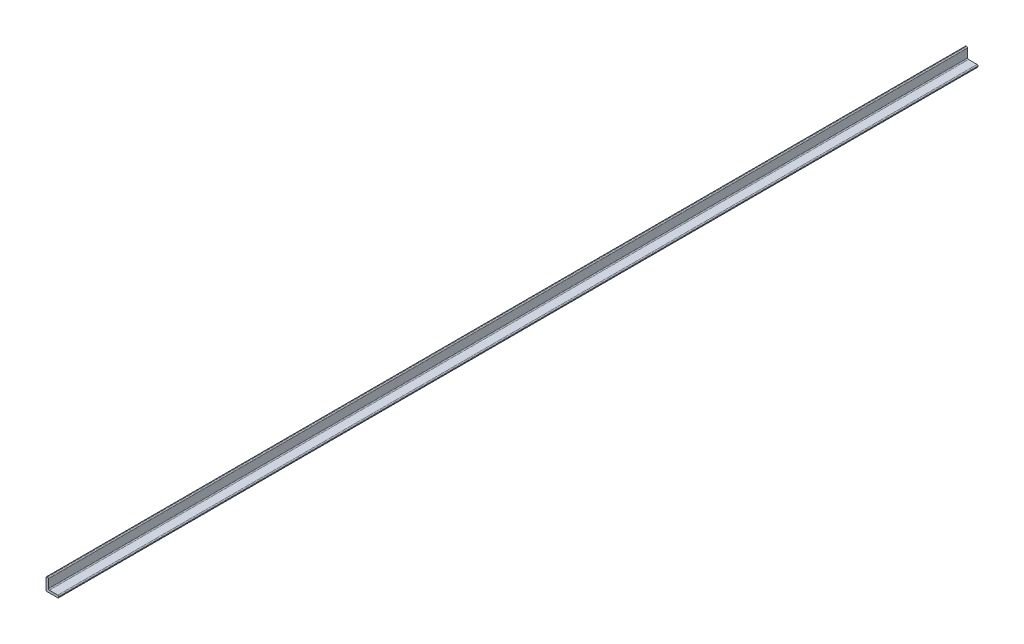
SolidWorks part; units mm, degrees
ref_plane "Front Plane" through (0, 0, 0) normal (0, 0, 1) x (1, 0, 0)
ref_plane "Top Plane" through (0, 0, 0) normal (0, 1, 0) x (1, 0, 0)
ref_plane "Right Plane" through (0, 0, 0) normal (1, 0, 0) x (0, 0, -1)
sketch "Sketch1" plane through (0, 0, 0) normal (0, 0, 1) x (1, 0, 0)
  line L0 (0, -12.7) -> (0, 12.7) construction
  line L1 (12.7, 0) -> (-12.7, 0) construction
  line L2 (-12.7, 12.7) -> (-12.7, -12.7) construction
  line L3 (-12.7, -12.7) -> (12.7, -12.7) construction
  line L4 (12.7, -12.7) -> (12.7, -7.9375) construction
  line L5 (12.7, -7.9375) -> (-7.9375, -7.9375) construction
  line L6 (-7.9375, -7.9375) -> (-7.9375, 12.7) construction
  line L7 (-7.9375, 12.7) -> (-12.7, 12.7) construction
  line L8 (-7.9375, -7.9375) -> (-12.7, -7.9375) construction
  line L9 (-7.9375, -7.9375) -> (-7.9375, -12.7) construction
  point P4 (0, 0)
  point P8 (0, 0)
  point P14 (12.7, -8.0645)
  dimension "Wall Thickness" = 4.7625
  dimension "Outside Height" = 25.4
  dimension "Outside Width" = 25.4
  dimension "Inside Width" = 20.6375
  dimension "Inside Height" = 20.6375
  dimension "Finish Thickness" = 0.254
sketch "Sketch2" plane through (0, 0, 0) normal (1, 0, 0) x (0, 0, -1)
  line L0 (914.4, 0) -> (-914.4, 0) construction
  line L1 (914.4, -12.7) -> (-914.4, -12.7) construction
  point P0 (-882.65, 0)
  point P4 (0, 0)
  point P5 (882.65, 0)
  point P9 (0, -12.7)
  dimension "Length" = 1828.8
  dimension "D1" = 31.75
  dimension "D2" = 31.75
sketch "Sketch4" plane through (0, 0, 0) normal (0, 0, 1) x (1, 0, 0)
  line L0 (-7.9375, -7.9375) -> (-7.9375, 12.7) construction
  line L1 (12.7, -7.9375) -> (-7.9375, -7.9375) construction
  line L2 (12.7, -12.7) -> (12.7, -7.9375) construction
  line L3 (-12.7, -12.7) -> (12.7, -12.7) construction
  line L4 (-12.7, 12.7) -> (-12.7, -12.7) construction
  line L5 (-7.9375, 12.7) -> (-12.7, 12.7) construction
  line L6 (-7.9375, -6.0325) -> (-7.9375, 12.7)
  line L7 (12.7, -7.9375) -> (-6.0325, -7.9375)
  line L8 (12.7, -12.7) -> (12.7, -7.9375)
  line L9 (-12.7, -12.7) -> (12.7, -12.7)
  line L10 (-12.7, 12.7) -> (-12.7, -12.7)
  line L11 (-7.9375, 12.7) -> (-12.7, 12.7)
  arc A0 (-7.9375, -6.0325) -> (-6.0325, -7.9375) centre (-6.0325, -6.0325) ccw
  dimension "D1" = 1.905
extrude "Boss-Extrude1" add sketch "Sketch4" against normal up to vertex (914.4 mm away) and the other way up to vertex (914.4 mm away) up to point (0, 0, -914.4) other way up to point (0, 0, 914.4)
fillet "Fillet1" radius 1.905 5 edges at (-12.7, -12.7, 0) (12.7, -12.7, 0) (12.7, -7.9375, 0) (-12.7, 12.7, 0) (-7.9375, 12.7, 0)
equation "\"D1@Sketch2\"=\"Outside Height@Sketch1\"*1.25"
equation "\"D2@Sketch2\"=\"D1@Sketch2\""
equation "\"D1@Sketch4\"=\"Wall Thickness@Sketch1\"/2.5"
equation "\"D1@Fillet1\"=\"D1@Sketch4\""
